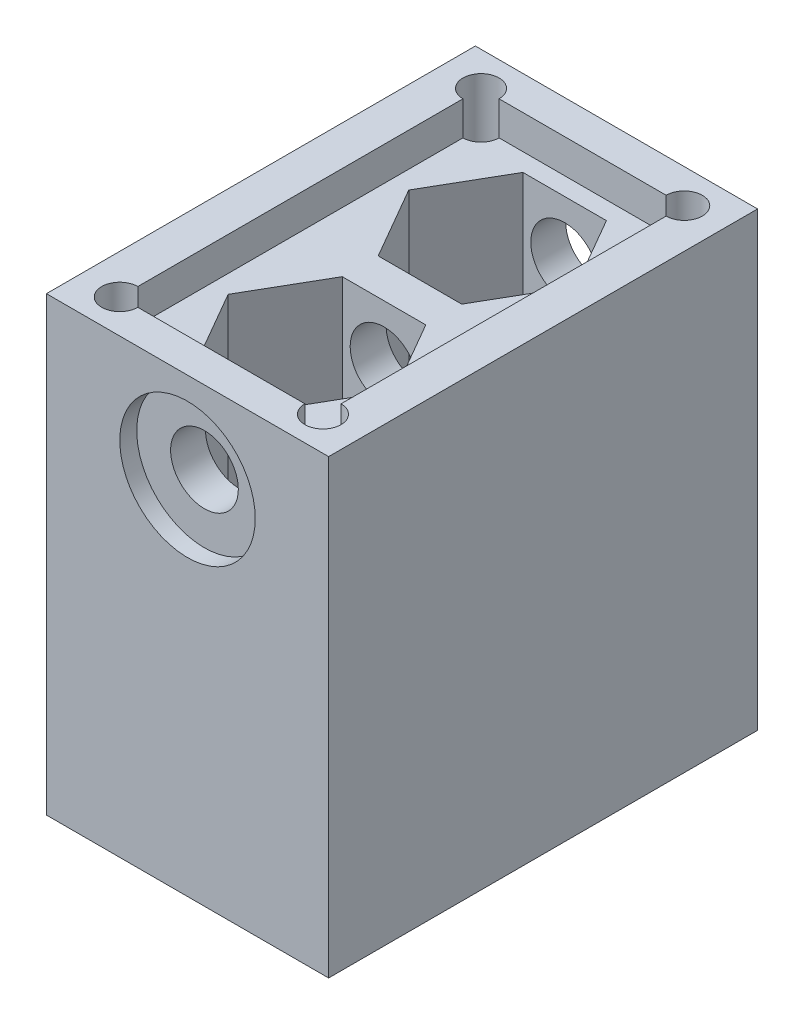
SolidWorks part; units mm, degrees
ref_plane "Спереди" through (0, 0, 0) normal (0, 0, 1) x (1, 0, 0)
ref_plane "Сверху" through (0, 0, 0) normal (0, 1, 0) x (1, 0, 0)
ref_plane "Справа" through (0, 0, 0) normal (1, 0, 0) x (0, 0, -1)
sketch "Sketch1" plane through (0, 0, 0) normal (0, 1, 0) x (1, 0, 0)
  line L1 (12.5, -19) -> (-12.5, -19)
  line L2 (12.5, -19) -> (12.5, 19)
  line L3 (12.5, 19) -> (-12.5, 19)
  line L4 (-12.5, -19) -> (-12.5, 19)
  line L5 (12.5, -19) -> (-12.5, 19) construction
  line L6 (12.5, 19) -> (-12.5, -19) construction
  point P0 (0, 0)
  dimension "D1" = 25
  dimension "D2" = 38
extrude "Boss-Extrude1" add sketch "Sketch1" along normal blind 40
sketch "Sketch2" plane through (0, 0, 19) normal (0, 0, 1) x (1, 0, 0)
  line L0 (-12.5, 32) -> (12.5, 32) construction
  line L1 (-12.5, 40) -> (-12.5, 0) construction
  line L2 (12.5, 40) -> (12.5, 0) construction
  line L3 (-12.5, 40) -> (12.5, 40) construction
  circle A0 centre (0, 32) radius 3
  dimension "D1" = 6
  dimension "D2" = 8
extrude "Cut-Extrude1" cut sketch "Sketch2" against normal through all
sketch "Sketch4" plane through (0, 40, 0) normal (0, 1, 0) x (1, 0, 0)
  line L0 (0, 19) -> (0, -19) construction
  line L1 (12.5, 19) -> (-12.5, 19) construction
  line L2 (-12.5, -19) -> (12.5, -19) construction
  circle A0 centre (0, -8) radius 4.15
  circle A1 centre (0, 8) radius 4.15
  point P3 (0, 0)
  dimension "D1" = 8.3
  dimension "D2" = 16
  dimension "D3" = 8
extrude "Cut-Extrude2" cut sketch "Sketch4" against normal through all
sketch "Sketch5" plane through (0, 40, 0) normal (0, 1, 0) x (1, 0, 0)
  line L1 (-3.7, -14.4086) -> (3.7, -14.4086)
  line L2 (3.7, -14.4086) -> (7.4, -8)
  line L3 (7.4, -8) -> (3.7, -1.5914)
  line L4 (3.7, -1.5914) -> (-3.7, -1.5914)
  line L5 (-3.7, -1.5914) -> (-7.4, -8)
  line L6 (-7.4, -8) -> (-3.7, -14.4086)
  line L7 (-12.5, -19) -> (12.5, -19) construction
  line L8 (-3.7, 14.4086) -> (-7.4, 8)
  line L9 (-7.4, 8) -> (-3.7, 1.5914)
  line L10 (-3.7, 1.5914) -> (3.7, 1.5914)
  line L11 (3.7, 1.5914) -> (7.4, 8)
  line L12 (7.4, 8) -> (3.7, 14.4086)
  line L13 (3.7, 14.4086) -> (-3.7, 14.4086)
  circle A0 centre (0, -8) radius 7.4 construction
  circle A1 centre (0, 8) radius 7.4 construction
  dimension "D1" = 14.8
extrude "Cut-Extrude3" cut sketch "Sketch5" against normal blind 18
sketch "Sketch6" plane through (0, 40, 0) normal (0, 1, 0) x (1, 0, 0)
  line L1 (-9, 16) -> (9, 16) construction
  line L2 (-9, 16) -> (-9, -16) construction
  line L3 (-9, -16) -> (9, -16) construction
  line L4 (9, 16) -> (9, -16) construction
  line L5 (-9, 16) -> (9, -16) construction
  line L6 (-9, -16) -> (9, 16) construction
  circle A0 centre (9, -16) radius 1.6
  circle A1 centre (-9, -16) radius 1.6
  circle A2 centre (-9, 16) radius 1.6
  circle A3 centre (9, 16) radius 1.6
  point P0 (0, 0)
  dimension "D1" = 3.2
  dimension "D2" = 18
  dimension "D3" = 32
extrude "Cut-Extrude4" cut sketch "Sketch6" against normal through all
sketch "Sketch7" plane through (0, 40, 0) normal (0, 1, 0) x (1, 0, 0)
  line L1 (-9, 16) -> (9, 16)
  line L2 (-9, 16) -> (-9, -16)
  line L3 (-9, -16) -> (9, -16)
  line L4 (9, 16) -> (9, -16)
  line L5 (-9, 16) -> (9, -16) construction
  line L6 (-9, -16) -> (9, 16) construction
  point P0 (0, 0)
  dimension "D1" = 18
extrude "Cut-Extrude5" cut sketch "Sketch7" against normal blind 3
sketch "Sketch8" plane through (0, 0, 0) normal (0, -1, 0) x (1, 0, 0)
  circle A0 centre (0, -8) radius 7.5 construction
  circle A1 centre (0, 8) radius 7.5 construction
  dimension "D1" = 15
sketch "Sketch9" plane through (0, 0, -19) normal (0, 0, -1) x (-1, 0, 0)
  circle A0 centre (0, 32) radius 6
  dimension "D1" = 12
extrude "Cut-Extrude6" cut sketch "Sketch9" against normal blind 1.5
sketch "Sketch10" plane through (0, 0, 19) normal (0, 0, 1) x (1, 0, 0)
  circle A0 centre (0, 32) radius 6
  dimension "D1" = 12
extrude "Cut-Extrude7" cut sketch "Sketch10" against normal blind 1.5
